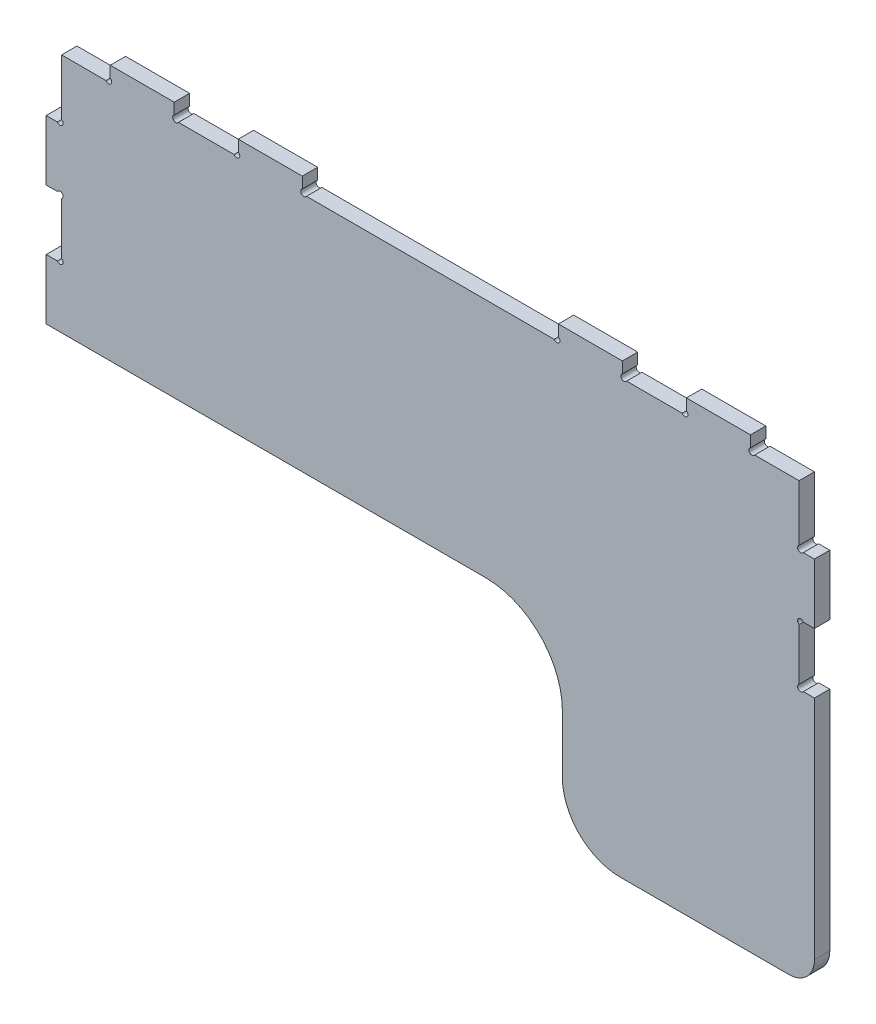
SolidWorks part; units mm, degrees
ref_plane "Front Plane" through (0, 0, 0) normal (0, 0, 1) x (1, 0, 0)
ref_plane "Top Plane" through (0, 0, 0) normal (0, 1, 0) x (1, 0, 0)
ref_plane "Right Plane" through (0, 0, 0) normal (1, 0, 0) x (0, 0, -1)
sketch "Sketch1" plane through (0, 0, 0) normal (0, 0, 1) x (1, 0, 0)
  line L0 (-298.0126, -63.3423) -> (45.1141, -63.3423)
  line L1 (-248.0126, 136.6577) -> (-198.0126, 136.6577)
  line L2 (-298.0126, 77.6577) -> (-298.0126, 30.6577)
  line L3 (150.1141, -213.3423) -> (277.389, -213.3423)
  line L4 (301.9874, 77.6577) -> (301.9874, 30.6577)
  line L5 (105.1141, -123.3423) -> (105.1141, -168.3423)
  line L6 (45.1141, -63.3423) -> (301.9874, -63.3423) construction
  line L7 (251.9874, 136.6577) -> (251.9874, 127.9361)
  line L8 (301.9874, -63.3423) -> (301.9874, -193.3423)
  line L9 (281.9874, -213.3423) -> (277.389, -213.3423)
  line L10 (226.9874, 136.6577) -> (226.9874, 122.2938) construction
  line L11 (201.9874, 136.6577) -> (201.9874, 127.9361)
  line L12 (198.7089, 124.6577) -> (155.2659, 124.6577)
  line L13 (151.9874, 127.9361) -> (151.9874, 136.6577)
  line L14 (201.9874, 136.6577) -> (251.9874, 136.6577)
  line L15 (101.9874, 136.6577) -> (101.9874, 127.9361)
  line L16 (98.7089, 124.6577) -> (-94.7341, 124.6577)
  line L17 (-148.0126, 136.6577) -> (-98.0126, 136.6577)
  line L18 (101.9874, 136.6577) -> (151.9874, 136.6577)
  line L19 (251.9874, 124.6577) -> (254.3874, 124.6577) construction
  line L20 (254.3874, 124.6577) -> (253.1874, 124.6577) construction
  line L21 (253.1874, 124.6577) -> (253.1874, 126.5373) construction
  line L22 (251.9874, 127.0577) -> (251.9874, 125.8577) construction
  line L23 (251.9874, 125.8577) -> (253.7601, 125.8577) construction
  line L24 (255.2659, 124.6577) -> (289.9874, 124.6577)
  line L25 (151.9874, 130.6577) -> (201.9874, 130.6577) construction
  line L26 (201.9874, 130.6577) -> (176.9874, 130.6577) construction
  line L27 (176.9874, 130.6577) -> (176.9874, 116.5546) construction
  line L28 (126.9874, 136.6577) -> (126.9874, 119.6446) construction
  line L29 (-298.0126, 44.1432) -> (301.9874, 44.1432) construction
  line L30 (1.9874, 44.1432) -> (1.9874, 143.1442) construction
  line L31 (-98.0126, 136.6577) -> (-98.0126, 127.9361)
  line L32 (-148.0126, 127.9361) -> (-148.0126, 136.6577)
  line L33 (-194.7341, 124.6577) -> (-151.2911, 124.6577)
  line L34 (-198.0126, 136.6577) -> (-198.0126, 127.9361)
  line L35 (-248.0126, 136.6577) -> (-248.0126, 127.9361)
  line L36 (-251.2911, 124.6577) -> (-286.0126, 124.6577)
  line L37 (-286.0126, 124.6577) -> (-286.0126, 80.9361)
  line L38 (-298.0126, 54.1577) -> (-275.0798, 54.1577) construction
  line L39 (-298.0126, 30.6577) -> (-289.2911, 30.6577)
  line L40 (-286.0126, 27.3792) -> (-286.0126, -13.0639)
  line L41 (-289.2911, -16.3423) -> (-298.0126, -16.3423)
  line L42 (-298.0126, -16.3423) -> (-298.0126, -63.3423)
  line L43 (-286.0126, 77.6577) -> (-288.4126, 77.6577) construction
  line L44 (-288.4126, 77.6577) -> (-287.2126, 77.6577) construction
  line L45 (-287.2126, 77.6577) -> (-287.2126, 79.3402) construction
  line L46 (-286.0126, 77.6577) -> (-286.0126, 80.0577) construction
  line L47 (-286.0126, 80.0577) -> (-286.0126, 78.8577) construction
  line L48 (-286.0126, 78.8577) -> (-287.574, 78.8577) construction
  line L49 (-289.2911, 77.6577) -> (-298.0126, 77.6577)
  line L50 (-298.0126, 30.6577) -> (-298.0126, -16.3423) construction
  line L51 (-298.0126, 7.1577) -> (-277.9339, 7.1577) construction
  line L52 (293.2659, -16.3423) -> (301.9874, -16.3423)
  line L53 (289.9874, 27.3792) -> (289.9874, -13.0639)
  line L54 (301.9874, 30.6577) -> (293.2659, 30.6577)
  line L55 (293.2659, 77.6577) -> (301.9874, 77.6577)
  line L56 (289.9874, 124.6577) -> (289.9874, 80.9361)
  line L57 (301.9874, -16.3423) -> (301.9874, -63.3423)
  arc A0 (45.1141, -63.3423) -> (105.1141, -123.3423) centre (45.1141, -123.3423) cw
  arc A1 (105.1141, -168.3423) -> (150.1141, -213.3423) centre (150.1141, -168.3423) ccw
  arc A2 (301.9874, -193.3423) -> (281.9874, -213.3423) centre (281.9874, -193.3423) cw
  circle A3 centre (251.9874, 124.6577) radius 2.4 construction
  arc A4 (251.9874, 127.9361) -> (255.2659, 124.6577) centre (253.1874, 125.8577) ccw
  arc A5 (201.9874, 127.9361) -> (198.7089, 124.6577) centre (200.7874, 125.8577) cw
  arc A6 (151.9874, 127.9361) -> (155.2659, 124.6577) centre (153.1874, 125.8577) ccw
  arc A7 (101.9874, 127.9361) -> (98.7089, 124.6577) centre (100.7874, 125.8577) cw
  arc A8 (-98.0126, 127.9361) -> (-94.7341, 124.6577) centre (-96.8126, 125.8577) ccw
  arc A9 (-148.0126, 127.9361) -> (-151.2911, 124.6577) centre (-149.2126, 125.8577) cw
  arc A10 (-198.0126, 127.9361) -> (-194.7341, 124.6577) centre (-196.8126, 125.8577) ccw
  arc A11 (-248.0126, 127.9361) -> (-251.2911, 124.6577) centre (-249.2126, 125.8577) cw
  circle A12 centre (-286.0126, 77.6577) radius 2.4 construction
  arc A13 (-289.2911, 77.6577) -> (-286.0126, 80.9361) centre (-287.2126, 78.8577) ccw
  arc A14 (-289.2911, 30.6577) -> (-286.0126, 27.3792) centre (-287.2126, 29.4577) cw
  arc A15 (-289.2911, -16.3423) -> (-286.0126, -13.0639) centre (-287.2126, -15.1423) ccw
  arc A16 (293.2659, -16.3423) -> (289.9874, -13.0639) centre (291.1874, -15.1423) cw
  arc A17 (293.2659, 30.6577) -> (289.9874, 27.3792) centre (291.1874, 29.4577) ccw
  arc A18 (293.2659, 77.6577) -> (289.9874, 80.9361) centre (291.1874, 78.8577) cw
  dimension "D4" = 60
  dimension "D2" = 45
  dimension "D5" = 20
  dimension "D11" = 4.8
  dimension "D12" = 4.8
  dimension "D16" = 4.8
  dimension "D17" = 4.8
  dimension "D3" = 200
  dimension "D6" = 12
  dimension "D7" = 50
  dimension "D8" = 12
  dimension "D10" = 50
  dimension "D13" = 47
  dimension "D15" = 47
extrude "Boss-Extrude1" add sketch "Sketch1" along normal blind 12
